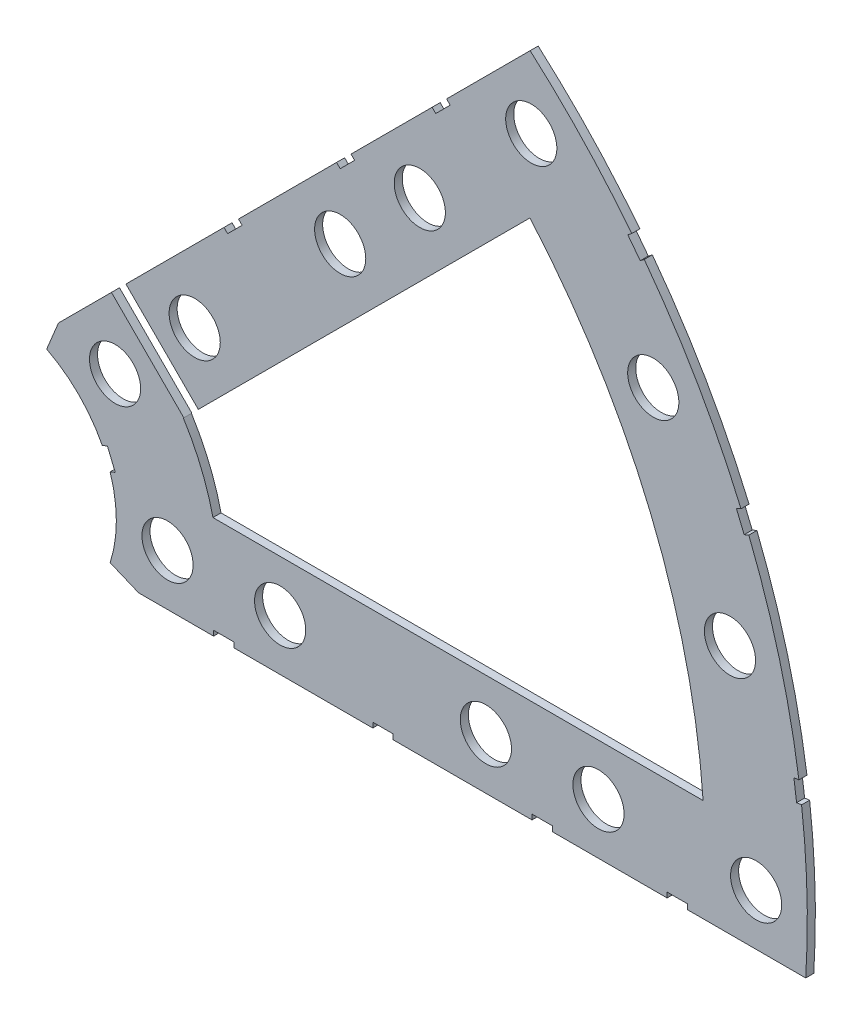
SolidWorks part; units mm, degrees
material "Copper"
ref_plane "Front Plane" through (0, 0, 0) normal (0, 0, 1) x (1, 0, 0)
ref_plane "Top Plane" through (0, 0, 0) normal (0, 1, 0) x (1, 0, 0)
ref_plane "Right Plane" through (0, 0, 0) normal (1, 0, 0) x (0, 0, -1)
sketch "Sketch1" plane through (0, 0, 0) normal (0, 0, 1) x (1, 0, 0)
  line L0 (0, 0) -> (320.3893, 0) construction
  line L1 (0, 0) -> (155.5285, 155.5285) construction
  line L2 (67.2115, 76.1917) -> (8.6967, 17.6769)
  line L3 (8.6967, 17.6769) -> (7.229, 14.1336)
  line L4 (101.4014, -6.35) -> (18.6489, -6.35)
  line L5 (15.1056, -4.8823) -> (18.6489, -6.35)
  line L6 (88.6729, 6.35) -> (27.8605, 6.35)
  line L9 (67.1914, 58.2111) -> (24.1905, 15.2102)
  line L10 (0, 0) -> (40.4486, 97.6516) construction
  line L11 (0, 0) -> (123.4567, -51.1374) construction
  line L18 (8.6967, 17.6769) -> (13.294, 8.6183) construction
  line L19 (18.6489, -6.35) -> (15.4943, 3.3063) construction
  line L20 (27.8605, 6.35) -> (27.7442, 6.7059) construction
  line L21 (24.1905, 15.2102) -> (24.3599, 14.8764) construction
  arc A0 (7.229, 14.1336) -> (15.1056, -4.8823) centre (0, 0) cw
  arc A1 (67.2115, 76.1917) -> (101.4014, -6.35) centre (0, 0) cw
  arc A2 (24.1905, 15.2102) -> (27.8605, 6.35) centre (0, 0) cw
  arc A3 (67.1914, 58.2111) -> (88.6729, 6.35) centre (0, 0) cw
  arc A8 (13.294, 8.6183) -> (15.4943, 3.3063) centre (0, 0) cw construction
  arc A9 (24.3599, 14.8764) -> (27.7442, 6.7059) centre (0, 0) cw construction
  dimension "D1" = 45
  dimension "D3" = 6.35
  dimension "D4" = 15.875
  dimension "D7" = 22.5
  dimension "D8" = 101.6
  dimension "D11" = 12.7
  dimension "D12" = 12.7
  dimension "D2" = 6.35
  dimension "D5" = 67.5
  dimension "D9" = 1.27
  dimension "D10" = 1.27
  dimension "D6" = 12.7
extrude "Boss-Extrude1" add sketch "Sketch1" along normal blind 1
sketch "Sketch2" plane through (0, 0, 1) normal (0, 0, 1) x (1, 0, 0)
  line L0 (0, 0) -> (101.6, 0) construction
  line L1 (0, 0) -> (71.842, 71.842) construction
  line L3 (0, 0) -> (22.225, 0) construction
  line L4 (0, 0) -> (15.7154, 15.7154) construction
  line L5 (0, 0) -> (95.25, 0) construction
  line L6 (0, 0) -> (92.0044, 24.6525) construction
  arc A0 (101.4014, -6.35) -> (67.2115, 76.1917) centre (0, 0) ccw construction
  circle A1 centre (22.225, 0) radius 3.175
  arc A2 (15.1056, -4.8823) -> (7.229, 14.1336) centre (0, 0) ccw construction
  circle A3 centre (36.195, 0) radius 3.175
  circle A4 centre (61.722, 0) radius 3.175
  circle A5 centre (75.692, 0) radius 3.175
  circle A6 centre (95.25, 0) radius 3.175
  circle A7 centre (15.7154, 15.7154) radius 3.175
  circle A8 centre (25.5937, 25.5937) radius 3.175
  circle A9 centre (43.644, 43.644) radius 3.175
  circle A10 centre (53.5223, 53.5223) radius 3.175
  circle A11 centre (92.0044, 24.6525) radius 3.175
  circle A12 centre (82.4889, 47.625) radius 3.175
  circle A13 centre (67.3519, 67.3519) radius 3.175
  dimension "D3" = 6.35
  dimension "D1" = 45
  dimension "D2" = 6.35
  dimension "D4" = 6.35
  dimension "D5" = 13.97
  dimension "D7" = 13.97
  dimension "D8" = 19.558
  dimension "D9" = 45
  dimension "D10" = 15
  dimension "D11" = 25.527
  dimension "D6" = 2
extrude "Cut-Extrude1" cut sketch "Sketch2" against normal through all
sketch "Sketch3" plane through (0, 0, 1) normal (0, 0, 1) x (1, 0, 0)
  line L0 (25.1447, 14.3684) -> (14.3684, 25.1447)
  line L1 (25.1447, 14.3684) -> (26.9408, 16.1645)
  line L2 (14.3684, 25.1447) -> (16.1645, 26.9408)
  line L3 (26.9408, 16.1645) -> (16.1645, 26.9408)
  line L4 (67.2115, 76.1917) -> (8.6967, 17.6769) construction
  line L5 (44.9911, 53.9713) -> (43.195, 52.1753)
  line L6 (44.9911, 53.9713) -> (45.4401, 53.5223)
  line L7 (43.195, 52.1753) -> (43.644, 51.7263)
  line L8 (45.4401, 53.5223) -> (43.644, 51.7263)
  line L9 (27.94, -6.35) -> (30.48, -6.35)
  line L10 (27.94, -6.35) -> (27.94, -5.715)
  line L11 (30.48, -6.35) -> (30.48, -5.715)
  line L12 (27.94, -5.715) -> (30.48, -5.715)
  line L13 (18.6489, -6.35) -> (101.4014, -6.35) construction
  line L14 (67.437, -6.35) -> (69.977, -6.35)
  line L15 (67.437, -6.35) -> (67.437, -5.715)
  line L16 (69.977, -6.35) -> (69.977, -5.715)
  line L17 (67.437, -5.715) -> (69.977, -5.715)
  line L18 (29.2307, 38.211) -> (31.0268, 40.007)
  line L19 (29.2307, 38.211) -> (29.6797, 37.762)
  line L20 (31.0268, 40.007) -> (31.4758, 39.558)
  line L21 (29.6797, 37.762) -> (31.4758, 39.558)
  line L22 (56.845, 65.8253) -> (55.049, 64.0292)
  line L23 (56.845, 65.8253) -> (57.294, 65.3763)
  line L24 (55.049, 64.0292) -> (55.498, 63.5802)
  line L25 (57.294, 65.3763) -> (55.498, 63.5802)
  line L26 (47.6885, -6.35) -> (50.2285, -6.35)
  line L27 (47.6885, -6.35) -> (47.6885, -5.715)
  line L28 (50.2285, -6.35) -> (50.2285, -5.715)
  line L29 (47.6885, -5.715) -> (50.2285, -5.715)
  line L30 (84.201, -6.35) -> (86.741, -6.35)
  line L31 (84.201, -6.35) -> (84.201, -5.715)
  line L32 (86.741, -6.35) -> (86.741, -5.715)
  line L33 (84.201, -5.715) -> (86.741, -5.715)
  line L34 (0, 0) -> (100.7308, 13.2615) construction
  line L35 (0, 0) -> (93.8662, 38.8806) construction
  line L36 (0, 0) -> (80.6047, 61.8502) construction
  line L37 (0, 0) -> (101.6, 0) construction
  line L38 (99.9355, 14.4377) -> (100.267, 11.9194)
  line L39 (99.9355, 14.4377) -> (101.1946, 14.6035)
  line L40 (100.267, 11.9194) -> (101.5261, 12.0852)
  line L41 (101.1946, 14.6035) -> (101.5261, 12.0852)
  line L42 (99.9355, 14.4377) -> (101.5261, 12.0852) construction
  line L43 (100.267, 11.9194) -> (101.1946, 14.6035) construction
  line L44 (93.7655, 37.4643) -> (94.9388, 37.9503)
  line L45 (93.7655, 37.4643) -> (92.7935, 39.811)
  line L46 (94.9388, 37.9503) -> (93.9668, 40.297)
  line L47 (92.7935, 39.811) -> (93.9668, 40.297)
  line L48 (93.7655, 37.4643) -> (93.9668, 40.297) construction
  line L49 (94.9388, 37.9503) -> (92.7935, 39.811) construction
  line L50 (79.3278, 62.4712) -> (80.874, 60.456)
  line L51 (79.3278, 62.4712) -> (80.3354, 63.2443)
  line L52 (80.874, 60.456) -> (81.8816, 61.2292)
  line L53 (80.3354, 63.2443) -> (81.8816, 61.2292)
  line L54 (79.3278, 62.4712) -> (81.8816, 61.2292) construction
  line L55 (80.874, 60.456) -> (80.3354, 63.2443) construction
  line L56 (13.5939, 7.0054) -> (14.5659, 4.6588)
  line L57 (13.5939, 7.0054) -> (14.7672, 7.4914)
  line L58 (14.5659, 4.6588) -> (15.7393, 5.1448)
  line L59 (14.7672, 7.4914) -> (15.7393, 5.1448)
  line L60 (13.5939, 7.0054) -> (15.7393, 5.1448) construction
  line L61 (14.5659, 4.6588) -> (14.7672, 7.4914) construction
  line L62 (25.1447, 14.3684) -> (16.1645, 26.9408) construction
  line L63 (14.3684, 25.1447) -> (26.9408, 16.1645) construction
  circle A0 centre (36.195, 0) radius 3.175 construction
  circle A1 centre (43.644, 43.644) radius 3.175 construction
  circle A2 centre (22.225, 0) radius 3.175 construction
  circle A3 centre (61.722, 0) radius 3.175 construction
  arc A4 (101.4014, -6.35) -> (67.2115, 76.1917) centre (0, 0) ccw construction
  arc A9 (15.1056, -4.8823) -> (7.229, 14.1336) centre (0, 0) ccw construction
  circle A10 centre (15.7154, 15.7154) radius 3.175 construction
  circle A11 centre (75.692, 0) radius 3.175 construction
  circle A12 centre (53.5223, 53.5223) radius 3.175 construction
  circle A13 centre (25.5937, 25.5937) radius 3.175 construction
  point P2 (20.6546, 20.6546)
  point P75 (14.6666, 6.0751)
  dimension "D6" = 5.715
  dimension "D8" = 0.635
  dimension "D9" = 5.715
  dimension "D12" = 5.715
  dimension "D4" = 7.5
  dimension "D5" = 22.5
  dimension "D7" = 37.5
  dimension "D10" = 90
  dimension "D11" = 1.27
  dimension "D14" = 0.635
  dimension "D15" = 90
  dimension "D18" = 0.635
  dimension "D19" = 90
  dimension "D22" = 0.635
  dimension "D20" = 1.27
  dimension "D17" = 0.635
  dimension "D3" = 2.54
  dimension "D21" = 2.54
  dimension "D25" = 15.24
  dimension "D26" = 90
  dimension "D27" = 5.715
  dimension "D28" = 6.35
  dimension "D13" = 11.4935
  dimension "D16" = 8.509
  dimension "D23" = 8.509
  dimension "D24" = 11.4935
extrude "Cut-Extrude2" cut sketch "Sketch3" against normal through all
equation "\"cSep\"= 1.005"
equation "\"cSep2\"= \"D8@Sketch2\""
equation "\"D13@Sketch3\"=\"cSep\"/2-.05"
equation "\"D16@Sketch3\"=\"cSep2\"/2-.05"
equation "\"D23@Sketch3\"=\"cSep2\"/2-.05"
equation "\"D24@Sketch3\"=\"cSep\"/2-.05"
equation "\"D11@Sketch2\"=\"cSep\""
